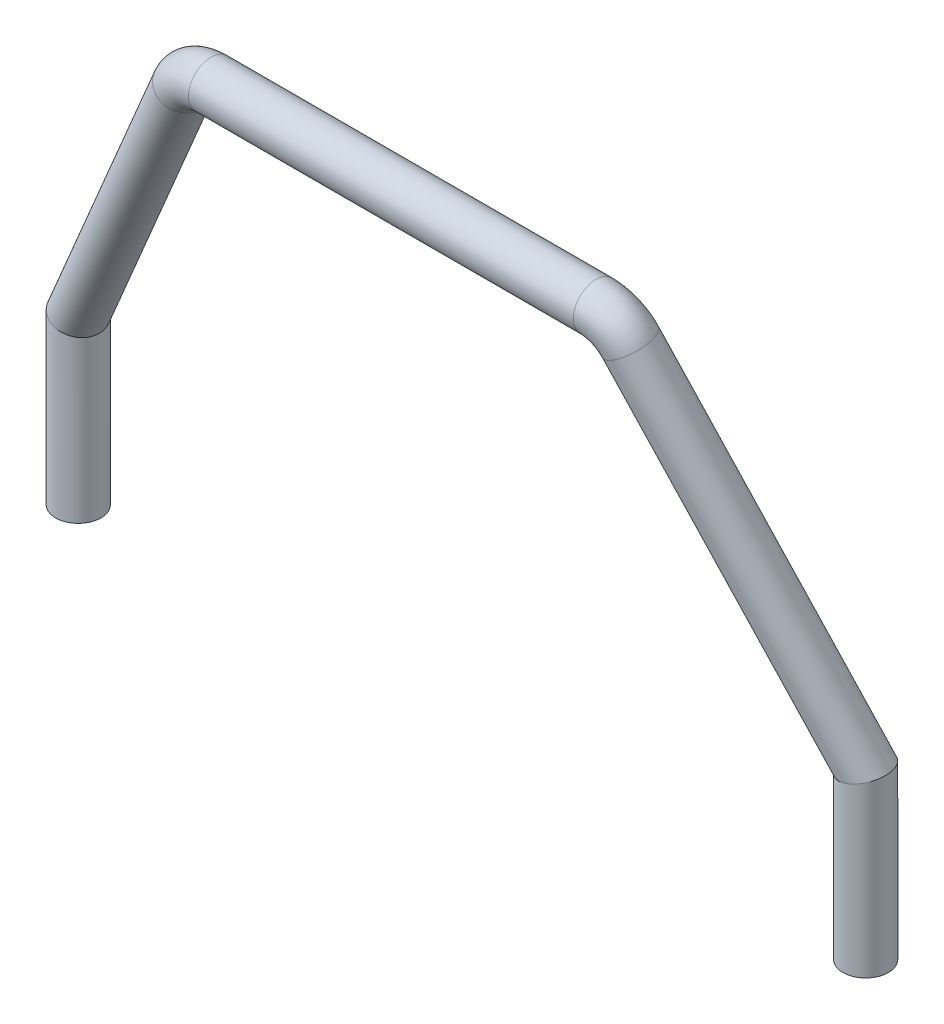
SolidWorks part; units mm, degrees
ref_plane "Front" through (0, 0, 0) normal (0, 0, 1) x (1, 0, 0)
ref_plane "Top" through (0, 0, 0) normal (0, 1, 0) x (1, 0, 0)
ref_plane "Right" through (0, 0, 0) normal (1, 0, 0) x (0, 0, -1)
sketch "Croquis1" plane through (0, 0, 0) normal (0, 0, 1) x (1, 0, 0)
  line L0 (-56.4, 0) -> (-56.4, -6.5473) construction
  line L1 (0, 0) -> (0, -15.0584) construction
  dimension "D1" = 56.4
sketch3d "Croquis3D1"
  line L0 (-56.4, 23.8578, 0) -> (-31.991, 69.0083, 9.2744)
  line L1 (-27.5724, 71.614, 9.8097) -> (0, 71.614, 9.8097)
  line L4 (-56.4, 0, 0) -> (-56.4, 23.8578, 0)
  arc A0 (-31.991, 69.0083, 9.2744) -> (-27.5724, 71.614, 9.8097) centre (-27.5724, 66.7162, 8.8036) ccw
  point P9 (-30.5824, 71.614, 9.8097)
  point P10 (-27.5724, 67.7223, 3.9059)
  dimension "D1" = 5
sketch "Croquis2" plane through (0, 0, 0) normal (0, 1, 0) x (1, 0, 0)
  circle A0 centre (-56.4, 0) radius 3.25
  dimension "D1" = 6.5
sweep "Barrer2" add profiles "Croquis2" path "Croquis3D1"
mirror "Simetría1" of "Barrer2"
